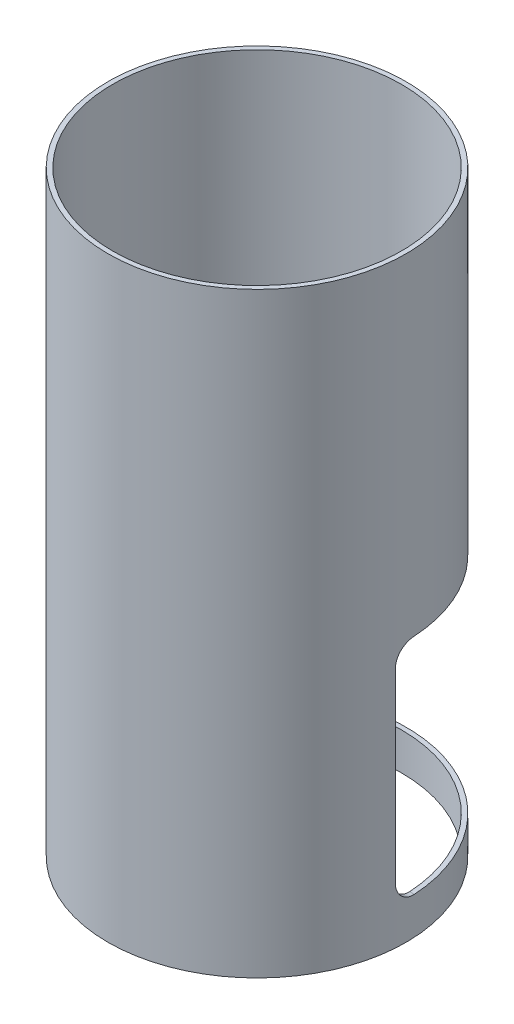
SolidWorks part; units mm, degrees
ref_plane "Front Plane" through (0, 0, 0) normal (0, 0, 1) x (1, 0, 0)
ref_plane "Top Plane" through (0, 0, 0) normal (0, 1, 0) x (1, 0, 0)
ref_plane "Right Plane" through (0, 0, 0) normal (1, 0, 0) x (0, 0, -1)
sketch "Sketch1" plane through (0, 0, 0) normal (0, 1, 0) x (1, 0, 0)
  circle A0 centre (0, 0) radius 98.425
  circle A1 centre (0, 0) radius 101.6
  dimension "D1" = 203.2
  dimension "D2" = 196.85
extrude "Boss-Extrude1" add sketch "Sketch1" along normal blind 406.4
sketch "Sketch3" plane through (0, 0, 0) normal (0, 1, 0) x (1, 0, 0)
  line L0 (0, 0) -> (101.3525, -7.0873)
  line L1 (0, 0) -> (-101.3525, -7.0873)
  line L2 (0, 0) -> (0, 101.6) construction
  circle A0 centre (0, 0) radius 101.6 construction
  circle A1 centre (0, 0) radius 98.425 construction
  circle A2 centre (0, 0) radius 98.425
  circle A3 centre (0, 0) radius 101.6
  dimension "D1" = 94
extrude "Cut-Extrude2" cut sketch "Sketch3" along normal blind 152.4 from offset 25.4 contours A2 L2 A3 L1 | L2 A2 L0 A3
fillet "Fillet1" radius 12.7 4 edges at (-99.7689, 25.4, 6.9765) (-99.7689, 177.8, 6.9765) (99.7689, 25.4, 6.9765) (99.7689, 177.8, 6.9765)
